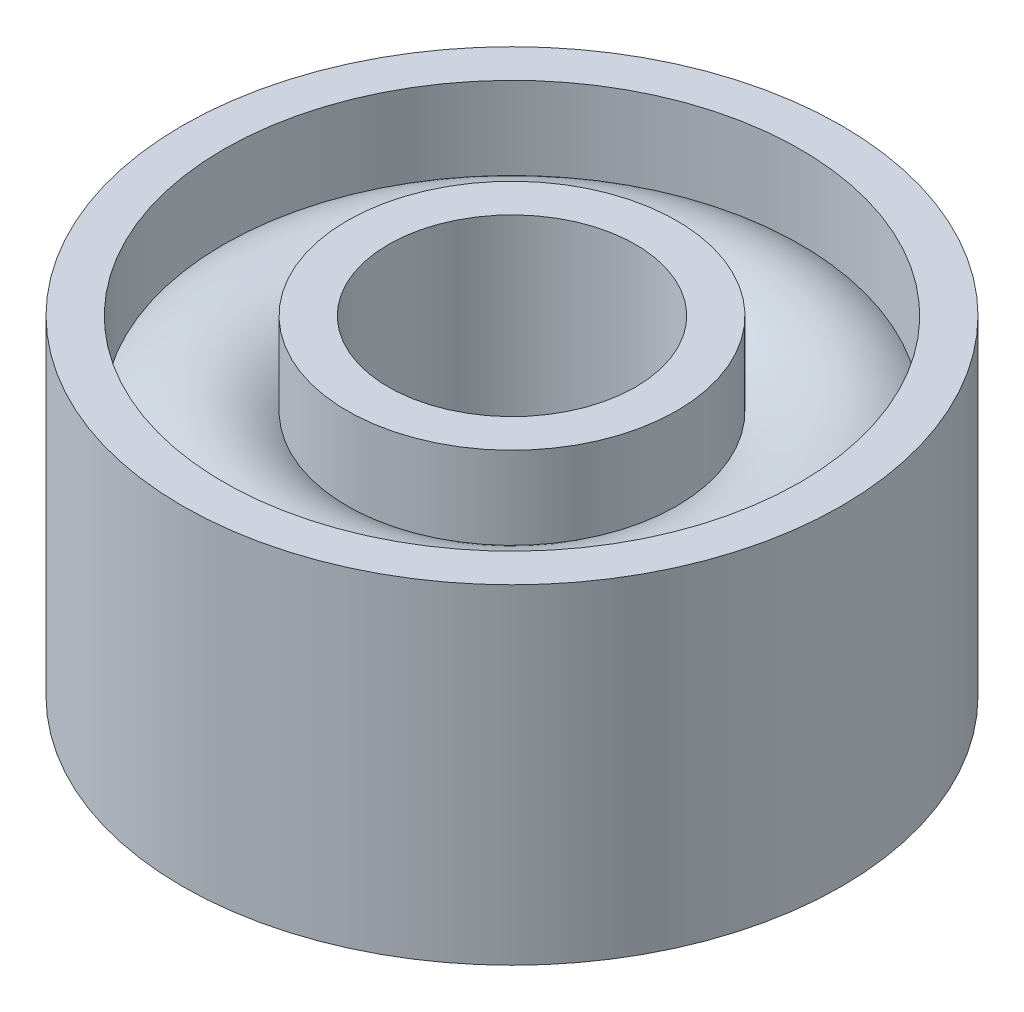
SolidWorks part; units mm, degrees
ref_plane "Front Plane" through (0, 0, 0) normal (0, 0, 1) x (1, 0, 0)
ref_plane "Top Plane" through (0, 0, 0) normal (0, 1, 0) x (1, 0, 0)
ref_plane "Right Plane" through (0, 0, 0) normal (1, 0, 0) x (0, 0, -1)
sketch "Sketch1" plane through (0, 0, 0) normal (0, 0, 1) x (1, 0, 0)
  line L0 (1.5, 2) -> (1.5, -2)
  line L1 (1.5, -2) -> (2, -2)
  line L2 (2, -2) -> (2, -1)
  line L3 (1.5, 2) -> (2, 2)
  line L4 (2, 2) -> (2, 1)
  line L5 (3.5, 1) -> (3.5, 2)
  line L6 (3.5, 2) -> (4, 2)
  line L7 (4, 2) -> (4, -2)
  line L8 (4, -2) -> (3.5, -2)
  line L9 (3.5, -2) -> (3.5, -1)
  line L10 (0, 1.3382) -> (0, -1.523) construction
  line L11 (1.5, 0) -> (4, 0) construction
  arc A0 (2, -1) -> (3.5, -1) centre (2.75, 0) ccw
  arc A1 (2, 1) -> (3.5, 1) centre (2.75, 0) cw
  point P3 (3.5127, 0.8321)
  point P16 (0, 0)
  point P20 (3.4345, 1.8792)
  point P21 (2.2231, -0.9746)
  point P22 (2.0947, 1.0645)
  dimension "D1" = 3
  dimension "D2" = 8
  dimension "D3" = 4
  dimension "D4" = 0.5
revolve "Revolve1" add sketch "Sketch1" angle 360 about L10
